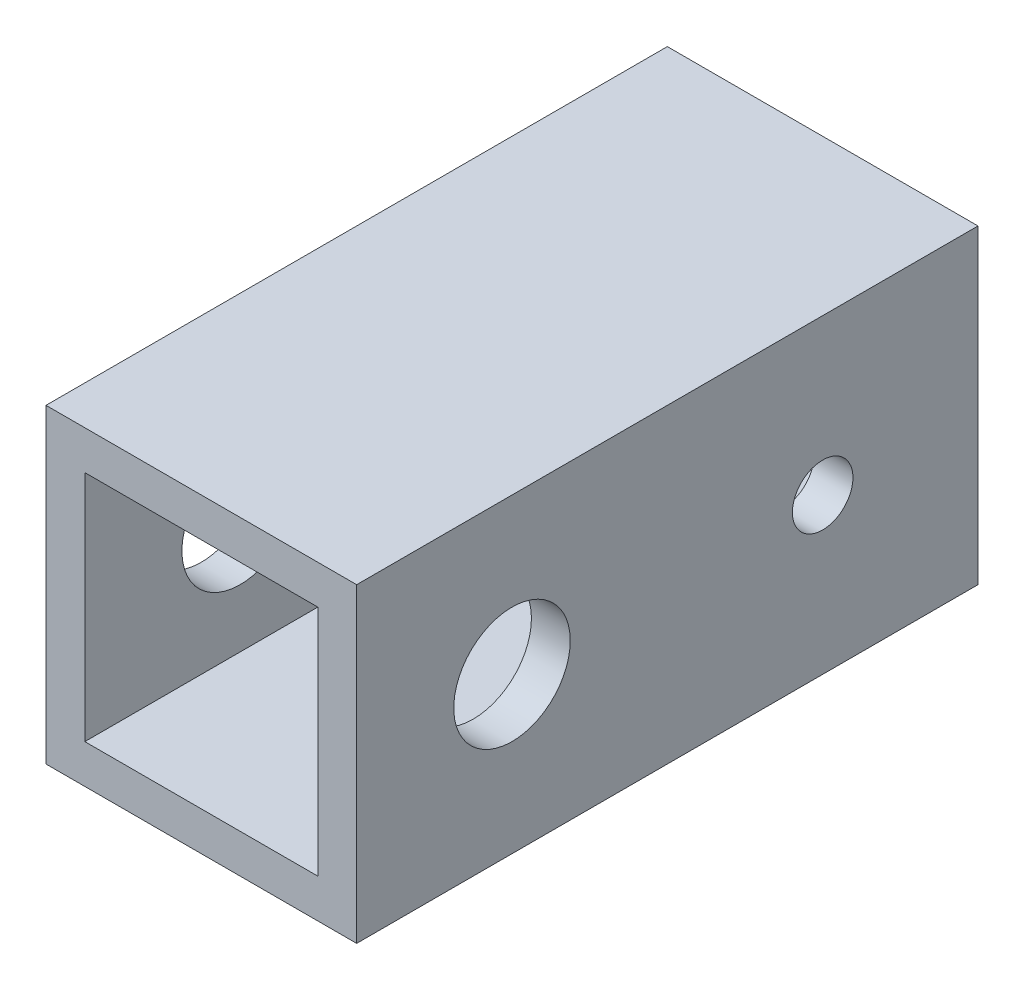
SolidWorks part; units mm, degrees
ref_plane "Front Plane" through (0, 0, 0) normal (0, 0, 1) x (1, 0, 0)
ref_plane "Top Plane" through (0, 0, 0) normal (0, 1, 0) x (1, 0, 0)
ref_plane "Right Plane" through (0, 0, 0) normal (1, 0, 0) x (0, 0, -1)
sketch "Sketch1" plane through (0, 0, 0) normal (0, 0, 1) x (1, 0, 0)
  line L1 (-12.7, -12.7) -> (12.7, -12.7)
  line L2 (-12.7, -12.7) -> (-12.7, 12.7)
  line L3 (-12.7, 12.7) -> (12.7, 12.7)
  line L4 (12.7, -12.7) -> (12.7, 12.7)
  line L5 (-12.7, -12.7) -> (12.7, 12.7) construction
  line L6 (-12.7, 12.7) -> (12.7, -12.7) construction
  point P0 (0, 0)
extrude "Extrude-Thin1" add sketch "Sketch1" along normal blind 50.8 thin thin type one direction reverse wall 3.175
sketch "Sketch2" plane through (12.7, 0, 0) normal (1, 0, 0) x (0, 0, -1)
  line L0 (-50.8, -12.7) -> (-50.8, 12.7) construction
  line L1 (-50.8, 12.7) -> (0, 12.7) construction
  line L2 (0, -12.7) -> (0, 12.7) construction
  line L4 (-50.8, -12.7) -> (0, -12.7) construction
  circle A0 centre (-38.1, 0) radius 4.7625
  circle A1 centre (-12.7, 0) radius 2.4765
  dimension "D1" = 12.7
  dimension "D3" = 12.7
  dimension "D5" = 9.525
  dimension "D6" = 4.953
  dimension "D2" = 12.7
  dimension "D4" = 12.7
extrude "Cut-Extrude1" cut sketch "Sketch2" against normal through all
